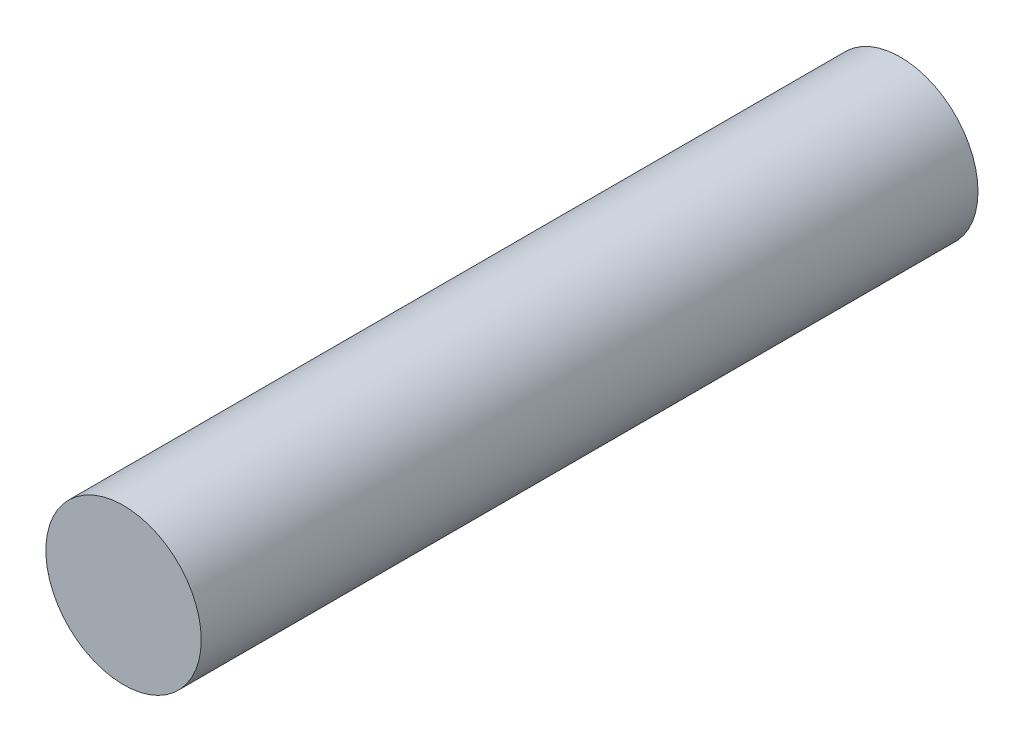
SolidWorks part; units mm, degrees
ref_plane "Front Plane" through (0, 0, 0) normal (0, 0, 1) x (1, 0, 0)
ref_plane "Top Plane" through (0, 0, 0) normal (0, 1, 0) x (1, 0, 0)
ref_plane "Right Plane" through (0, 0, 0) normal (1, 0, 0) x (0, 0, -1)
sketch "Sketch2" plane through (0, 0, 0) normal (0, 0, 1) x (1, 0, 0)
  circle A0 centre (0, 0) radius 1.5
extrude "Boss-Extrude1" add sketch "Sketch2" along normal blind 15
